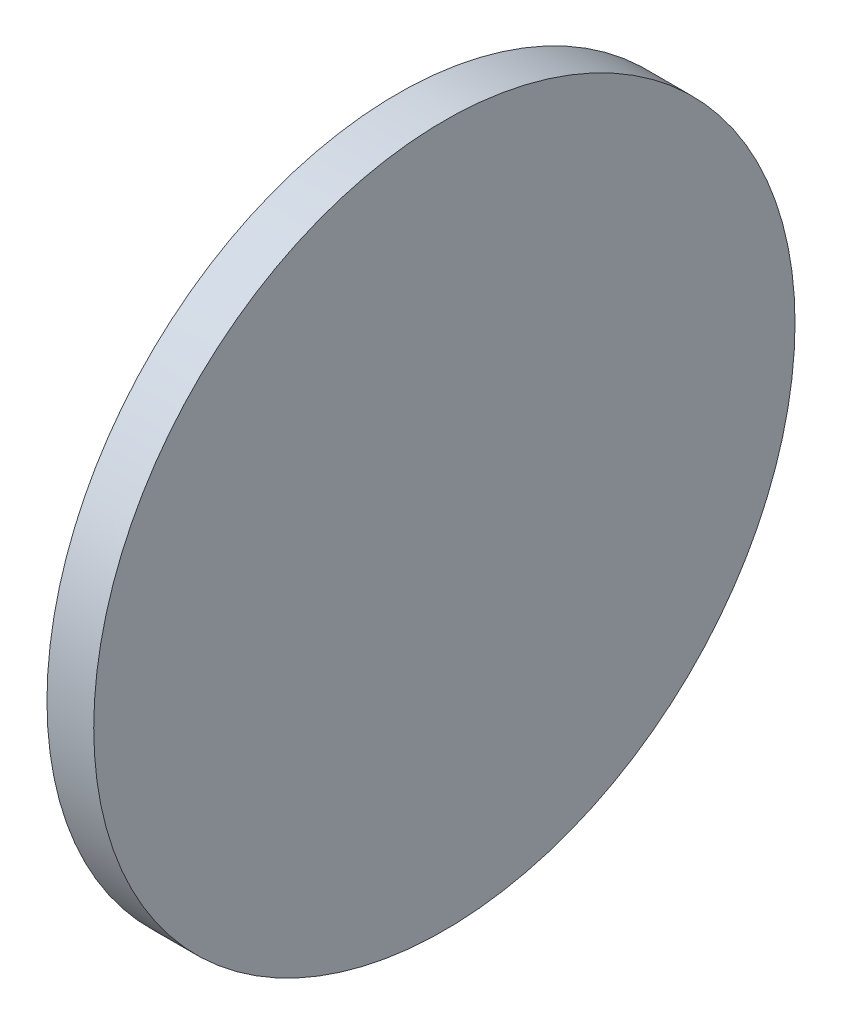
SolidWorks part; units mm, degrees
ref_plane "前视基准面" through (0, 0, 0) normal (0, 0, 1) x (1, 0, 0)
ref_plane "上视基准面" through (0, 0, 0) normal (0, 1, 0) x (1, 0, 0)
ref_plane "右视基准面" through (0, 0, 0) normal (1, 0, 0) x (0, 0, -1)
sketch "草图1" plane through (0, 0, 0) normal (0, 0, 1) x (1, 0, 0)
  line L0 (254.0008, 77.2932) -> (269.054, 77.2932) construction
  line L1 (260.1163, 77.2932) -> (260.1163, 92.2932)
  line L2 (260.1163, 92.2932) -> (262.1163, 92.2932)
  line L3 (262.1163, 92.2932) -> (262.1163, 77.2932)
  line L4 (262.1163, 77.2932) -> (260.1163, 77.2932)
revolve "旋转1" add sketch "草图1" angle 360 about L0
